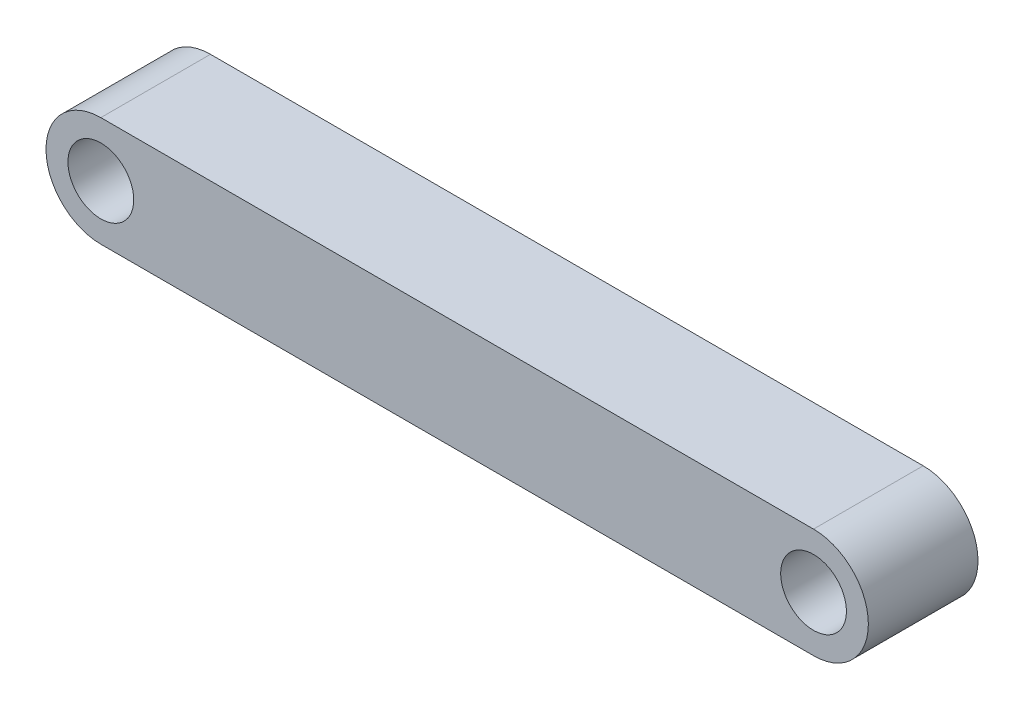
SolidWorks part; units mm, degrees
material "Acrylic (Medium-high impact)"
ref_plane "Front Plane" through (0, 0, 0) normal (0, 0, 1) x (1, 0, 0)
ref_plane "Top Plane" through (0, 0, 0) normal (0, 1, 0) x (1, 0, 0)
ref_plane "Right Plane" through (0, 0, 0) normal (1, 0, 0) x (0, 0, -1)
sketch "Sketch1" plane through (0, 0, 0) normal (0, 0, 1) x (1, 0, 0)
  line L0 (-26.3333, 0) -> (6.1667, 0) construction
  line L1 (-26.3333, 2.5) -> (6.1667, 2.5)
  line L2 (-26.3333, -2.5) -> (6.1667, -2.5)
  line L3 (-10.0833, 2.5) -> (-10.0833, -2.5) construction
  arc A0 (-26.3333, 2.5) -> (-26.3333, -2.5) centre (-26.3333, 0) ccw
  arc A1 (6.1667, -2.5) -> (6.1667, 2.5) centre (6.1667, 0) ccw
  circle A2 centre (-26.3333, 0) radius 1.5
  circle A3 centre (6.1667, 0) radius 1.5
  point P3 (-10.0833, 0)
  point P8 (-28.8333, 0)
  dimension "D3" = 1
  dimension "D4" = 3
  dimension "D1" = 5
  dimension "D2" = 35
extrude "Boss-Extrude1" add sketch "Sketch1" along normal blind 5
